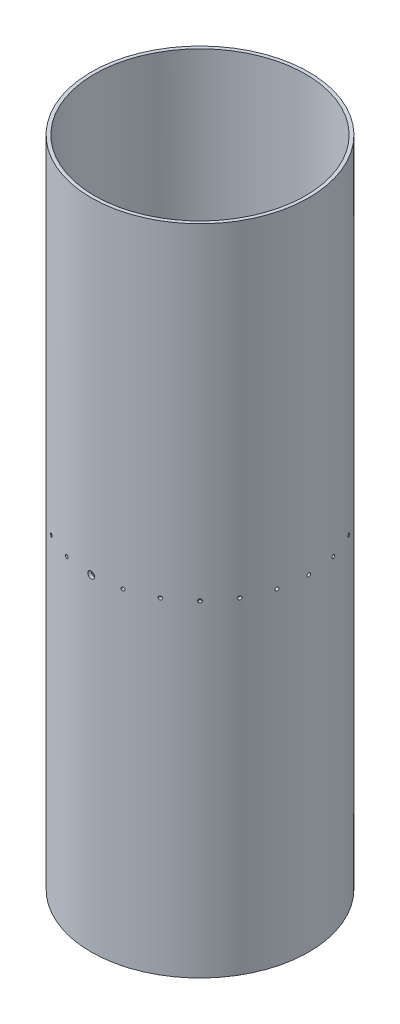
SolidWorks part; units mm, degrees
ref_plane "Front Plane" through (0, 0, 0) normal (0, 0, 1) x (1, 0, 0)
ref_plane "Top Plane" through (0, 0, 0) normal (0, 1, 0) x (1, 0, 0)
ref_plane "Right Plane" through (0, 0, 0) normal (1, 0, 0) x (0, 0, -1)
sketch "Sketch1" plane through (0, 0, 0) normal (0, 1, 0) x (1, 0, 0)
  circle A0 centre (0, 0) radius 101.6
  circle A1 centre (0, 0) radius 98.425
  dimension "D1" = 203.2
  dimension "D2" = 196.85
extrude "Boss-Extrude1" add sketch "Sketch1" along normal blind 609.6
sketch "Sketch2" plane through (0, 0, 0) normal (0, 0, 1) x (1, 0, 0)
  circle A0 centre (0, 304.8) radius 3.175
  dimension "D2" = 6.35
extrude "Cut-Extrude1" cut sketch "Sketch2" against normal through all and the other way through all
sketch "Sketch3" plane through (0, 0, 0) normal (1, 0, 0) x (0, 0, -1)
  circle A0 centre (0, 304.8) radius 1.5875
  dimension "D2" = 3.175
extrude "Cut-Extrude2" cut sketch "Sketch3" against normal blind 609.6
sketch "Sketch4" plane through (0, 0, 0) normal (0, 0, 1) x (1, 0, 0)
  line L0 (0, 0) -> (0, 635.0243) construction
pattern_circular "CirPattern1" count 24 over 360 about axis through (0, 0, 0) along (0, 1, 0) of "Cut-Extrude2"
sketch "Sketch5" plane through (0, 0, 0) normal (0, 0, 1) x (1, 0, 0)
  circle A1 centre (-84.7725, 422.8998) radius 2.1247
extrude "Cut-Extrude3" cut sketch "Sketch5" against normal through all and the other way through all
